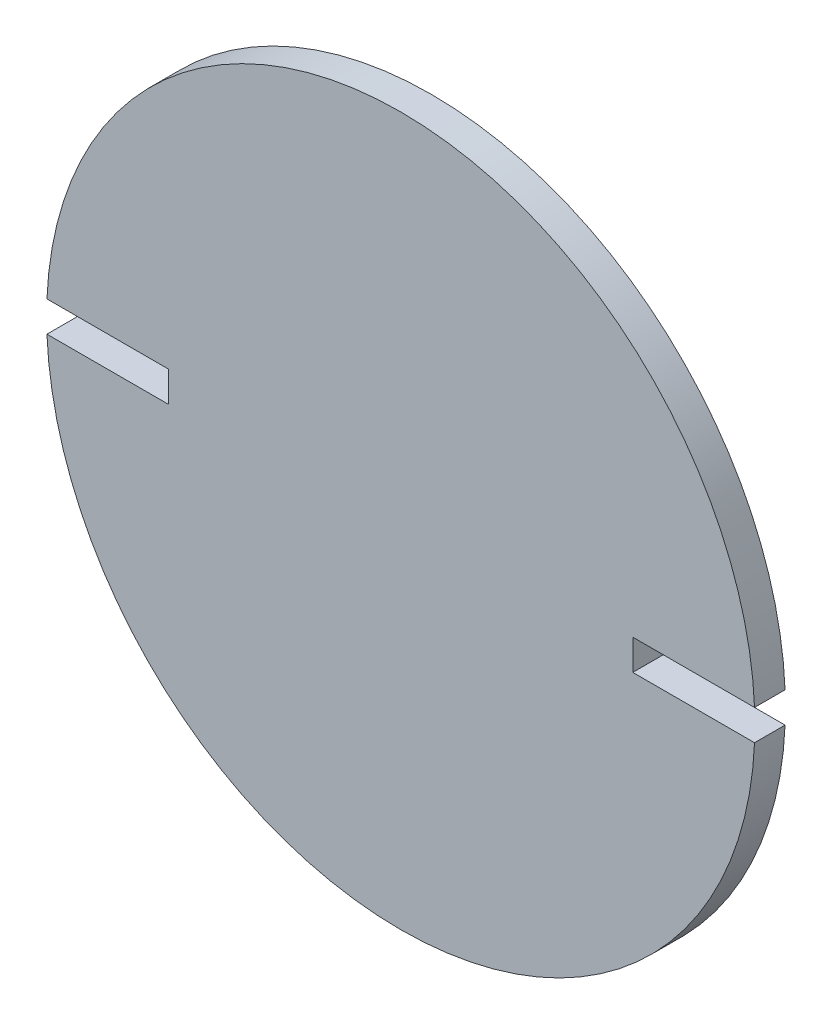
SolidWorks part; units mm, degrees
material "E-Glass Fiber"
ref_plane "Front Plane" through (0, 0, 0) normal (0, 0, 1) x (1, 0, 0)
ref_plane "Top Plane" through (0, 0, 0) normal (0, 1, 0) x (1, 0, 0)
ref_plane "Right Plane" through (0, 0, 0) normal (1, 0, 0) x (0, 0, -1)
sketch "Sketch1" plane through (0, 0, 0) normal (0, 0, 1) x (1, 0, 0)
  circle A0 centre (0, 0) radius 73.66
  dimension "D1" = 147.32
extrude "Boss-Extrude1" add sketch "Sketch1" along normal blind 6.35
sketch "Sketch2" plane through (0, 0, 0) normal (0, 0, -1) x (-1, 0, 0)
  line L0 (-76.2, 0) -> (73.66, 0) construction
  line L1 (-48.26, 0) -> (-48.26, 3.175)
  line L2 (-48.26, 3.175) -> (-76.2, 3.175)
  line L3 (-76.2, 3.175) -> (-76.2, -3.175)
  line L4 (-76.2, -3.175) -> (-48.26, -3.175)
  line L5 (-48.26, -3.175) -> (-48.26, 0)
  line L6 (0, 35.7336) -> (0, -26.6213) construction
  line L7 (48.26, -3.175) -> (48.26, 0)
  line L8 (48.26, 0) -> (48.26, 3.175)
  line L9 (76.2, -3.175) -> (48.26, -3.175)
  line L10 (76.2, 3.175) -> (76.2, -3.175)
  line L11 (48.26, 3.175) -> (76.2, 3.175)
  circle A0 centre (0, 0) radius 73.66 construction
  point P21 (-48.26, 1.5875)
  dimension "D1" = 6.35
  dimension "D2" = 27.94
  dimension "D3" = 48.26
extrude "Cut-Extrude1" cut sketch "Sketch2" against normal through all
